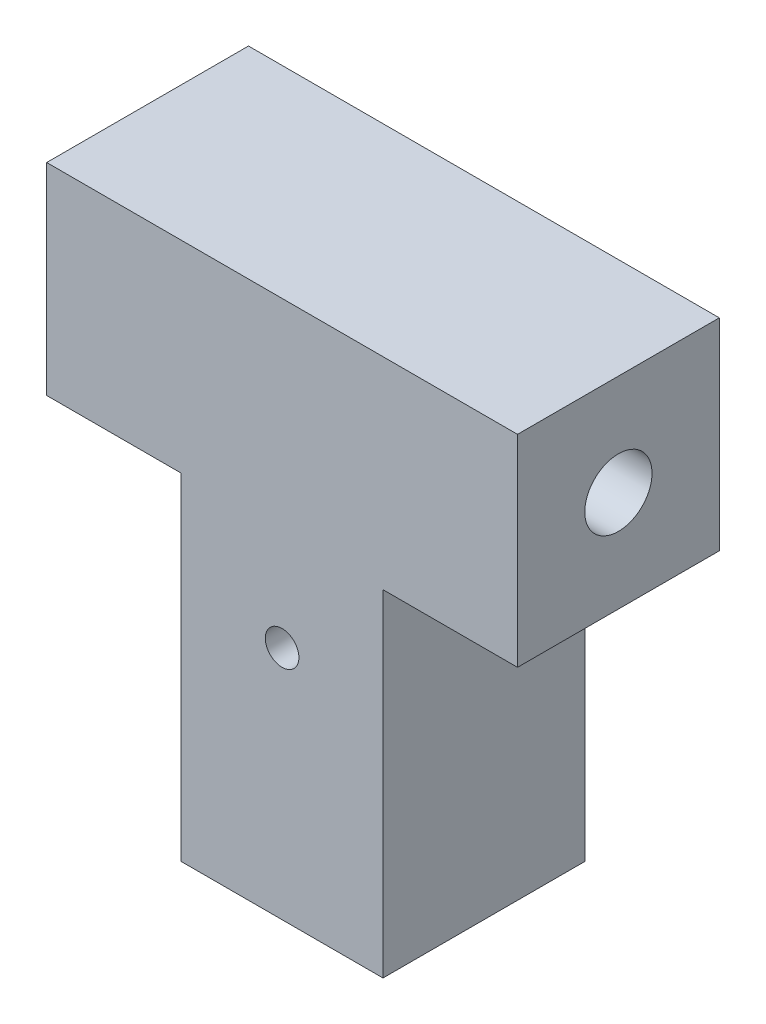
SolidWorks part; units mm, degrees
ref_plane "Спереди" through (0, 0, 0) normal (0, 0, 1) x (1, 0, 0)
ref_plane "Сверху" through (0, 0, 0) normal (0, 1, 0) x (1, 0, 0)
ref_plane "Справа" through (0, 0, 0) normal (1, 0, 0) x (0, 0, -1)
sketch "Эскиз1" plane through (0, 0, 0) normal (0, 1, 0) x (1, 0, 0)
  line L1 (6, -6) -> (-6, -6)
  line L2 (6, -6) -> (6, 6)
  line L3 (6, 6) -> (-6, 6)
  line L4 (-6, -6) -> (-6, 6)
  line L5 (6, -6) -> (-6, 6) construction
  line L6 (6, 6) -> (-6, -6) construction
  point P0 (0, 0)
  dimension "D1" = 12
extrude "Бобышка-Вытянуть1" add sketch "Эскиз1" along normal blind 20
sketch "Эскиз2" plane through (0, 20, 0) normal (0, 1, 0) x (1, 0, 0)
  line L1 (14, -6) -> (-14, -6)
  line L2 (14, -6) -> (14, 6)
  line L3 (14, 6) -> (-14, 6)
  line L4 (-14, -6) -> (-14, 6)
  line L5 (14, -6) -> (-14, 6) construction
  line L6 (14, 6) -> (-14, -6) construction
  point P0 (0, 0)
  dimension "D1" = 12
  dimension "D2" = 28
extrude "Бобышка-Вытянуть2" add sketch "Эскиз2" along normal blind 12
sketch "Эскиз3" plane through (0, 0, 0) normal (0, -1, 0) x (1, 0, 0)
  circle A0 centre (0, 0) radius 2.5
extrude "Вырез-Вытянуть1" cut sketch "Эскиз3" against normal blind 20
sketch "Эскиз4" plane through (0, 0, 6) normal (0, 0, 1) x (1, 0, 0)
  line L0 (0, 32) -> (0, 0) construction
  line L1 (-14, 32) -> (14, 32) construction
  line L2 (-6, 0) -> (6, 0) construction
  circle A0 centre (0, 14) radius 1
  dimension "D1" = 14
extrude "Вырез-Вытянуть2" cut sketch "Эскиз4" against normal through all
sketch "Эскиз5" plane through (-14, 0, 0) normal (-1, 0, 0) x (0, 0, 1)
  line L0 (0, 32) -> (0, 20) construction
  line L1 (-6, 32) -> (6, 32) construction
  line L2 (-6, 20) -> (6, 20) construction
  circle A0 centre (0, 26) radius 2
extrude "Вырез-Вытянуть3" cut sketch "Эскиз5" against normal through all
